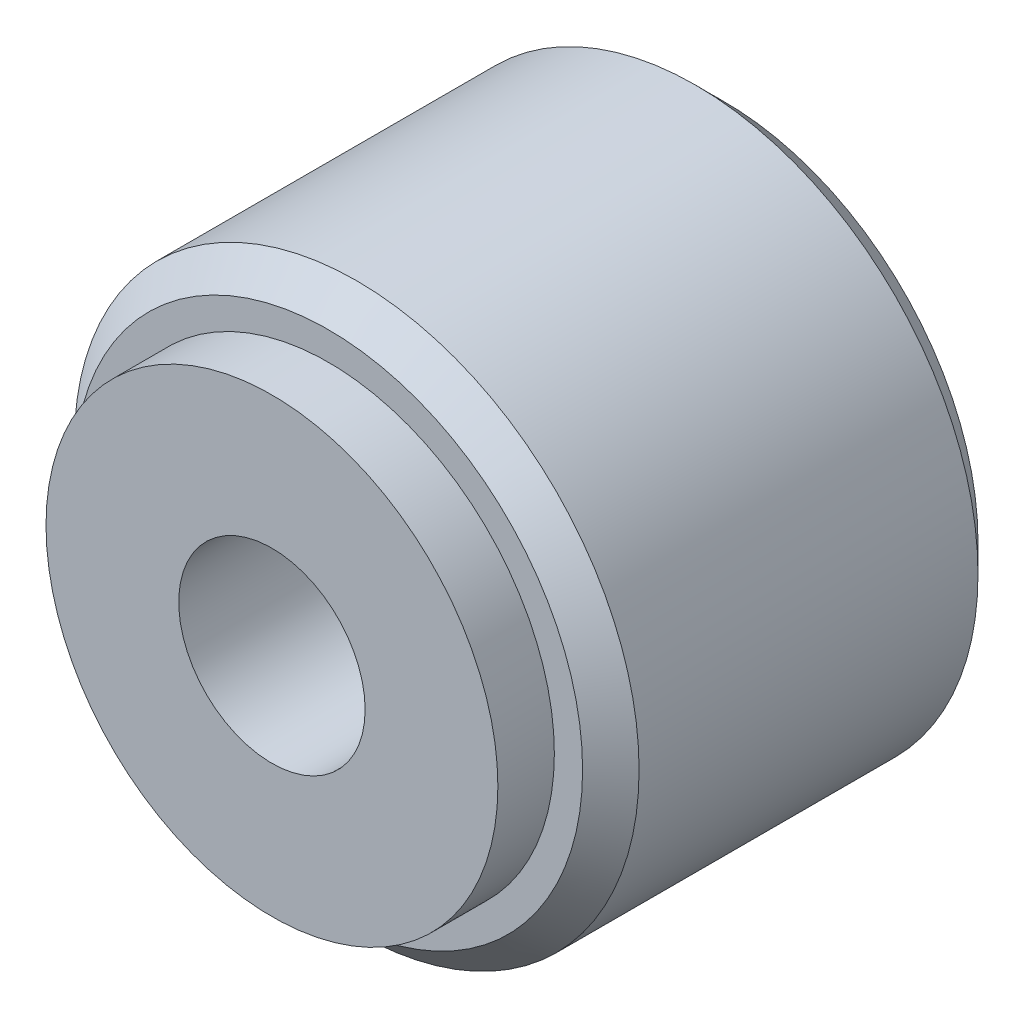
SolidWorks part; units mm, degrees
ref_plane "Спереди" through (0, 0, 0) normal (0, 0, 1) x (1, 0, 0)
ref_plane "Сверху" through (0, 0, 0) normal (0, 1, 0) x (1, 0, 0)
ref_plane "Справа" through (0, 0, 0) normal (1, 0, 0) x (0, 0, -1)
sketch "Эскиз1" plane through (0, 0, 0) normal (0, 0, 1) x (1, 0, 0)
  circle A0 centre (0, 0) radius 5
  dimension "D1" = 10
extrude "Бобышка-Вытянуть1" add sketch "Эскиз1" along normal blind 7
sketch "Эскиз2" plane through (0, 0, 7) normal (0, 0, 1) x (1, 0, 0)
  circle A0 centre (0, 0) radius 4
  dimension "D1" = 8
extrude "Бобышка-Вытянуть2" add sketch "Эскиз2" along normal blind 1
hole_wizard "Отверстие обработанное метчиком M4x0.71" positions "Эскиз4" profile "Эскиз3" tap size "M4x0.7" standard "Ansi Metric"
sketch "Эскиз4" plane through (0, 0, 8) normal (0, 0, 1) x (1, 0, 0)
  point P0 (0, 0)
sketch "Эскиз3" plane through (0, 0, 8) normal (1, 0, 0) x (0, -1, 0)
  line L0 (0, 0) -> (0, 6.7914)
  line L1 (0, 6.7914) -> (1.65, 5.8)
  line L2 (1.65, 5.8) -> (1.65, 0)
  line L5 (1.65, 0) -> (0, 0)
  line L10 (0, 6.7914) -> (-1.65, 5.8) construction
  line L11 (0, -6.35) -> (0, 107.95) construction
  dimension "Диаметр сверла" = 3.3
  dimension "Глубина сверла" = 5.8
  dimension "Угол заточки сверла" = 118
cosmetic thread "Отверстие резьбы1" parameters "D1"=3.3, "D2"=4
chamfer "Фаска1" distance 0.5 angle 45 2 edges at (5, 0, 7) (5, 0, 0)
